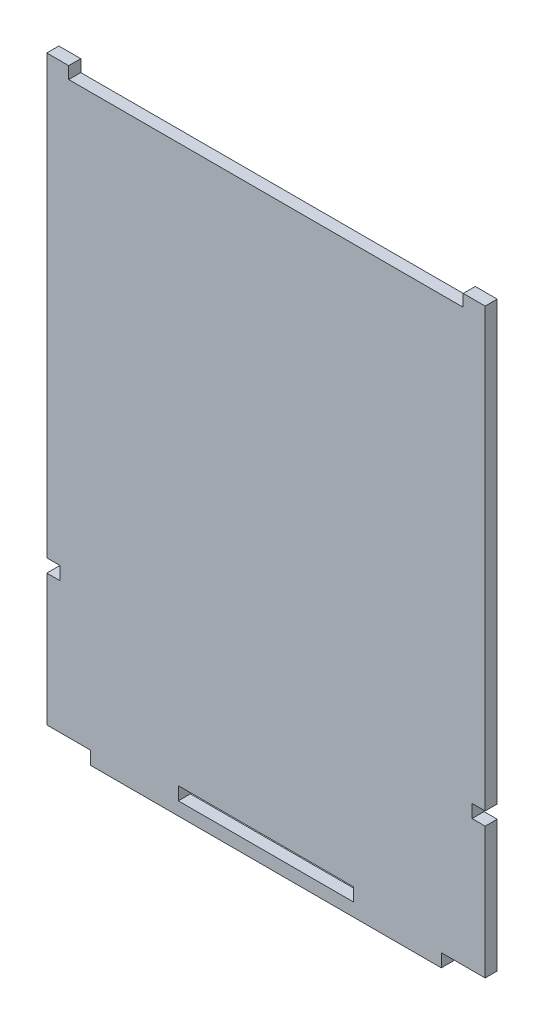
SolidWorks part; units mm, degrees
ref_plane "前视基准面" through (0, 0, 0) normal (0, 0, 1) x (1, 0, 0)
ref_plane "上视基准面" through (0, 0, 0) normal (0, 1, 0) x (1, 0, 0)
ref_plane "右视基准面" through (0, 0, 0) normal (1, 0, 0) x (0, 0, -1)
sketch "草图1" plane through (0, 0, 0) normal (0, 0, 1) x (1, 0, 0)
  line L0 (0, -30) -> (10, -30)
  line L1 (0, 0) -> (100, 0)
  line L2 (0, 3) -> (0, 100)
  line L3 (0, 100) -> (100, 100)
  line L4 (100, 3) -> (100, 100)
  line L5 (0, 0) -> (100, 0)
  line L6 (0, 0) -> (0, -30)
  line L7 (0, -30) -> (100, -30)
  line L8 (100, 0) -> (100, -30)
  line L9 (0, 0) -> (3, 0)
  line L11 (0, 3) -> (3, 3)
  line L12 (3, 0) -> (3, 3)
  line L13 (100, 0) -> (97, 0)
  line L15 (100, 3) -> (97, 3)
  line L16 (97, 0) -> (97, 3)
  line L17 (10, -30) -> (90, -30)
  line L18 (90, -30) -> (100, -30)
  line L19 (50, -30) -> (50, -27)
  line L20 (10, -30) -> (90, -30)
  line L21 (10, -30) -> (10, -33)
  line L22 (10, -33) -> (90, -33)
  line L23 (90, -30) -> (90, -33)
  line L24 (50, -27) -> (70, -27)
  line L25 (70, -27) -> (70, -30)
  line L26 (70, -30) -> (50, -30)
  line L27 (50, -27) -> (30, -27)
  line L28 (30, -27) -> (30, -30)
  line L29 (30, -30) -> (50, -30)
  line L30 (0, 100) -> (0, 102.75)
  line L31 (0, 102.75) -> (5, 102.75)
  line L32 (5, 102.75) -> (5, 100)
  line L33 (100, 100) -> (100, 102.75)
  line L34 (100, 102.75) -> (95, 102.75)
  line L35 (95, 102.4496) -> (95, 100)
  line L36 (95, 102.75) -> (95, 100)
extrude "凸台-拉伸1" add sketch "草图1" along normal blind 2.75 contours L34 L36 L35 L3 L33 | L5 L16 L15 L4 L3 L2 L11 L12 | L32 L31 L30 L3 | L28 L27 L24 L25 L20 L7 L8 L1 L5 L6 L0 | L23 L20 L17 L7 L21 L22
